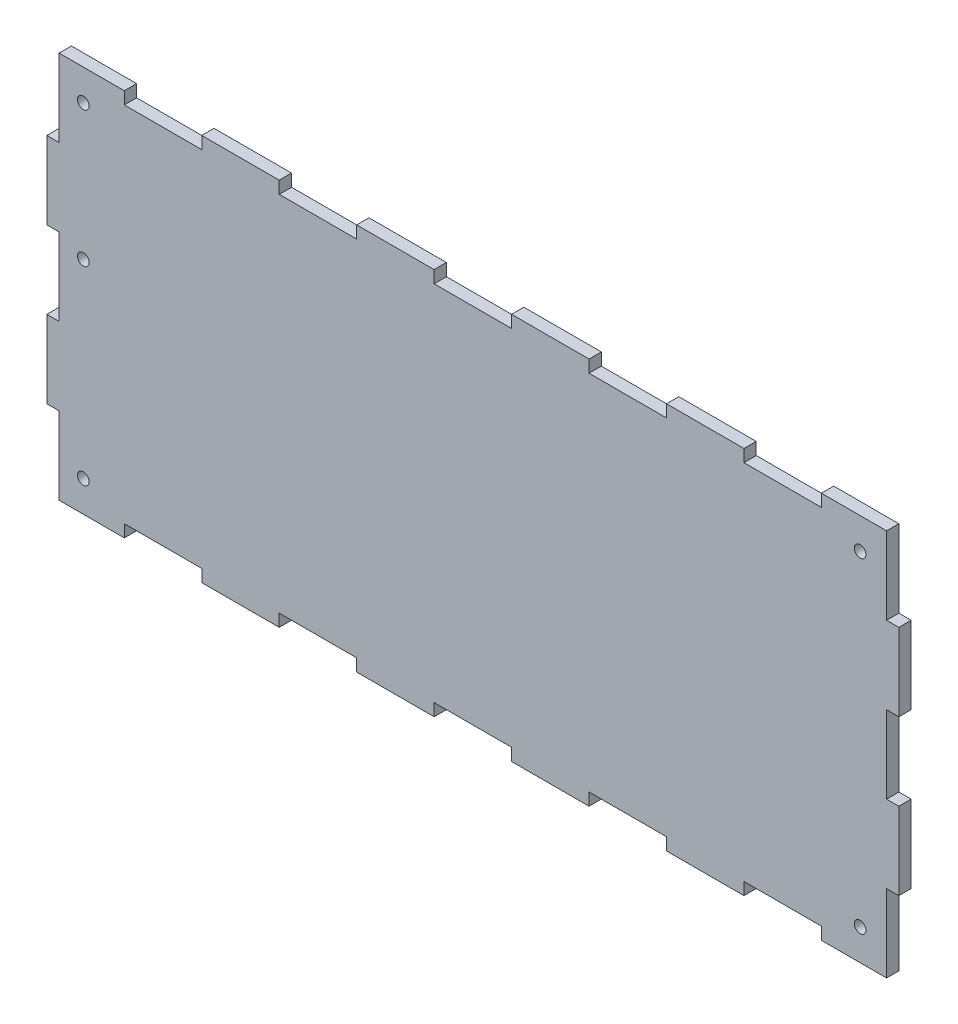
SolidWorks part; units mm, degrees
material "Acrylic (Medium-high impact)"
ref_plane "Front Plane" through (0, 0, 0) normal (0, 0, 1) x (1, 0, 0)
ref_plane "Top Plane" through (0, 0, 0) normal (0, 1, 0) x (1, 0, 0)
ref_plane "Right Plane" through (0, 0, 0) normal (1, 0, 0) x (0, 0, -1)
sketch "Sketch51" plane through (0, 0, 0) normal (0, 0, -1) x (-1, 0, 0)
  line L7 (-110, -49.9999) -> (110, -49.9999)
  line L8 (110, -49.9999) -> (110, 50)
  line L9 (-110, -49.9999) -> (-110, 50)
  line L10 (-110, 50) -> (110, 50)
  circle A1 centre (100.5876, -41.9999) radius 1.5
  circle A2 centre (100.5876, 42) radius 1.5
  circle A3 centre (-100, -41.9999) radius 1.5
  circle A4 centre (-100, 42) radius 1.5
  circle A5 centre (100.5876, 7.0001) radius 1.5
extrude "Boss-Extrude13" add sketch "Sketch51" along normal blind 3.175 separate body
sketch "Sketch52" plane through (0, 0, -3.175) normal (0, 0, -1) x (-1, 0, 0)
  line L0 (110, 10) -> (110, -10)
  line L2 (110, 10) -> (106.825, 10)
  line L3 (106.825, 10) -> (106.825, -10)
  line L4 (110, 50) -> (106.825, 50)
  line L5 (110, 50) -> (110, 30)
  line L6 (110, 30) -> (106.825, 30)
  line L7 (106.825, 50) -> (106.825, 30)
  line L8 (110, -10) -> (106.825, -10)
  line L9 (110, -30) -> (110, -50)
  line L10 (110, -30) -> (106.825, -30)
  line L11 (106.825, -30) -> (106.825, -50)
  line L12 (110, -50) -> (106.825, -50)
  line L13 (-110, 10) -> (-110, -10)
  line L14 (-110, 30) -> (-106.825, 30)
  line L15 (-110, 10) -> (-106.825, 10)
  line L16 (-106.825, 10) -> (-106.825, -10)
  line L17 (-110, 50) -> (-106.825, 50)
  line L18 (-110, 50) -> (-110, 30)
  line L20 (-106.825, 50) -> (-106.825, 30)
  line L21 (-110, -10) -> (-106.825, -10)
  line L22 (-110, -30) -> (-110, -50)
  line L23 (-110, -30) -> (-106.825, -30)
  line L24 (-106.825, -30) -> (-106.825, -50)
  line L25 (-110, -50) -> (-106.825, -50)
  line L26 (50, 50) -> (50, 46.825)
  line L28 (50, 50) -> (30, 50)
  line L29 (30, 50) -> (30, 46.825)
  line L30 (90, 50) -> (70, 50)
  line L31 (90, 50) -> (90, 46.825)
  line L32 (90, 46.825) -> (70, 46.825)
  line L33 (70, 50) -> (70, 46.825)
  line L34 (50, 46.825) -> (30, 46.825)
  line L35 (10, 50) -> (10, 46.825)
  line L36 (10, 50) -> (-10, 50)
  line L37 (-10, 50) -> (-10, 46.825)
  line L38 (10, 46.825) -> (-10, 46.825)
  line L39 (-30, 50) -> (-30, 46.825)
  line L40 (-30, 50) -> (-50, 50)
  line L41 (-50, 50) -> (-50, 46.825)
  line L42 (-30, 46.825) -> (-50, 46.825)
  line L43 (-70, 50) -> (-70, 46.825)
  line L44 (-70, 50) -> (-90, 50)
  line L45 (-90, 50) -> (-90, 46.825)
  line L46 (-70, 46.825) -> (-90, 46.825)
  line L47 (50, -49.9999) -> (50, -46.8249)
  line L49 (50, -49.9999) -> (30, -49.9999)
  line L50 (30, -49.9999) -> (30, -46.8249)
  line L51 (90, -49.9999) -> (70, -49.9999)
  line L52 (90, -49.9999) -> (90, -46.8249)
  line L53 (90, -46.8249) -> (70, -46.8249)
  line L54 (70, -49.9999) -> (70, -46.8249)
  line L55 (50, -46.8249) -> (30, -46.8249)
  line L56 (10, -49.9999) -> (10, -46.8249)
  line L57 (10, -49.9999) -> (-10, -49.9999)
  line L58 (-10, -49.9999) -> (-10, -46.8249)
  line L59 (10, -46.8249) -> (-10, -46.8249)
  line L60 (-30, -49.9999) -> (-30, -46.8249)
  line L61 (-30, -49.9999) -> (-50, -49.9999)
  line L62 (-50, -49.9999) -> (-50, -46.8249)
  line L63 (-30, -46.8249) -> (-50, -46.8249)
  line L64 (-70, -49.9999) -> (-70, -46.8249)
  line L65 (-70, -49.9999) -> (-90, -49.9999)
  line L66 (-90, -49.9999) -> (-90, -46.8249)
  line L67 (-70, -46.8249) -> (-90, -46.8249)
  point P3 (0, 0)
  dimension "D1" = 3
  dimension "D2" = 3
  dimension "D3" = 5
  dimension "D4" = 5
extrude "Cut-Extrude25" cut sketch "Sketch52" against normal blind 3.175
